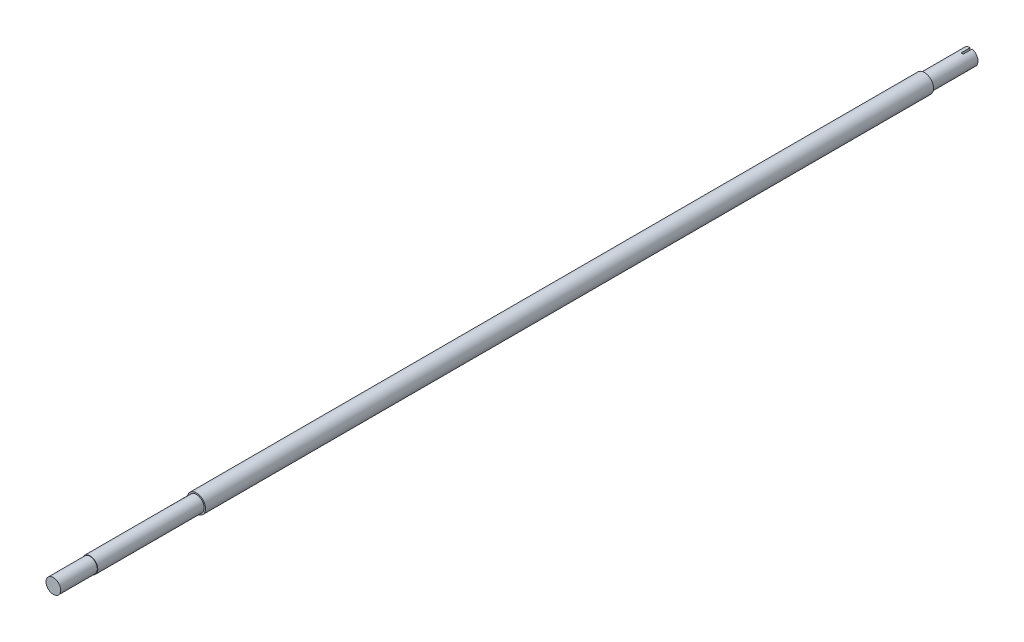
SolidWorks part; units mm, degrees
ref_plane "Piano frontale" through (0, 0, 0) normal (0, 0, 1) x (1, 0, 0)
ref_plane "Piano superiore" through (0, 0, 0) normal (0, 1, 0) x (1, 0, 0)
ref_plane "Piano destro" through (0, 0, 0) normal (1, 0, 0) x (0, 0, -1)
sketch "Schizzo1" plane through (0, 0, 0) normal (0, 0, 1) x (1, 0, 0)
  circle A0 centre (0, 0) radius 10
  dimension "D1" = 20
extrude "Estrusione-Estrusione1" add sketch "Schizzo1" along normal blind 1000
sketch "Schizzo2" plane through (0, 0, 1000) normal (0, 0, 1) x (1, 0, 0)
  circle A0 centre (0, 0) radius 8.5
  dimension "D1" = 17
extrude "Taglio-Estrusione3" cut sketch "Schizzo2" against normal blind 156 flip side to cut
sketch "Schizzo3" plane through (0, 0, 0) normal (0, 0, -1) x (-1, 0, 0)
  circle A0 centre (0, 0) radius 8.5
  dimension "D1" = 17
extrude "Taglio-Estrusione4" cut sketch "Schizzo3" against normal blind 50 flip side to cut
sketch "Schizzo6" plane through (0, 0, 1000) normal (0, 0, 1) x (1, 0, 0)
  circle A0 centre (0, 0) radius 8
  dimension "D1" = 16
extrude "Taglio-Estrusione6" cut sketch "Schizzo6" against normal blind 40 flip side to cut
sketch "Schizzo7" plane through (0, 0, 0) normal (0, 0, -1) x (-1, 0, 0)
  line L1 (0, 0) -> (-2.1405, 0)
  line L2 (0, 0) -> (0, 11.0588)
  line L3 (0, 11.0588) -> (-2.1405, 11.0588)
  line L4 (-2.1405, 0) -> (-2.1405, 11.0588)
extrude "Taglio-Estrusione11" cut sketch "Schizzo7" against normal blind 10
